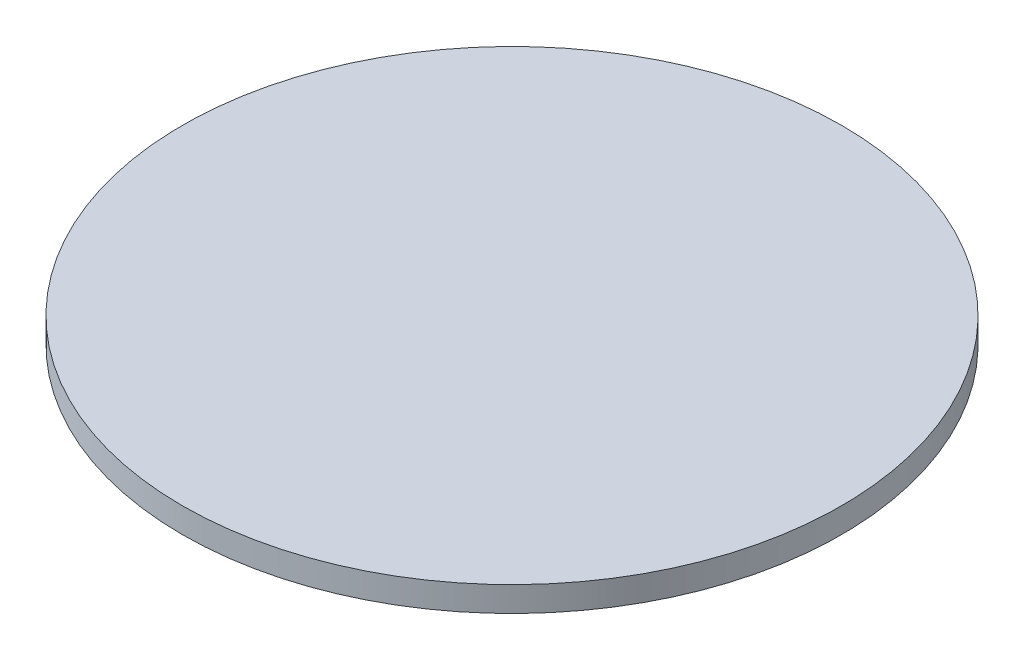
SolidWorks part; units mm, degrees
ref_plane "前视基准面" through (0, 0, 0) normal (0, 0, 1) x (1, 0, 0)
ref_plane "上视基准面" through (0, 0, 0) normal (0, 1, 0) x (1, 0, 0)
ref_plane "右视基准面" through (0, 0, 0) normal (1, 0, 0) x (0, 0, -1)
sketch "草图1" plane through (0, 0, 0) normal (0, 1, 0) x (1, 0, 0)
  circle A0 centre (0, 0) radius 23.7
  circle A1 centre (0, 0) radius 24 construction
  dimension "D1" = 0.3
extrude "凸台-拉伸1" add sketch "草图1" along normal blind 1.8
